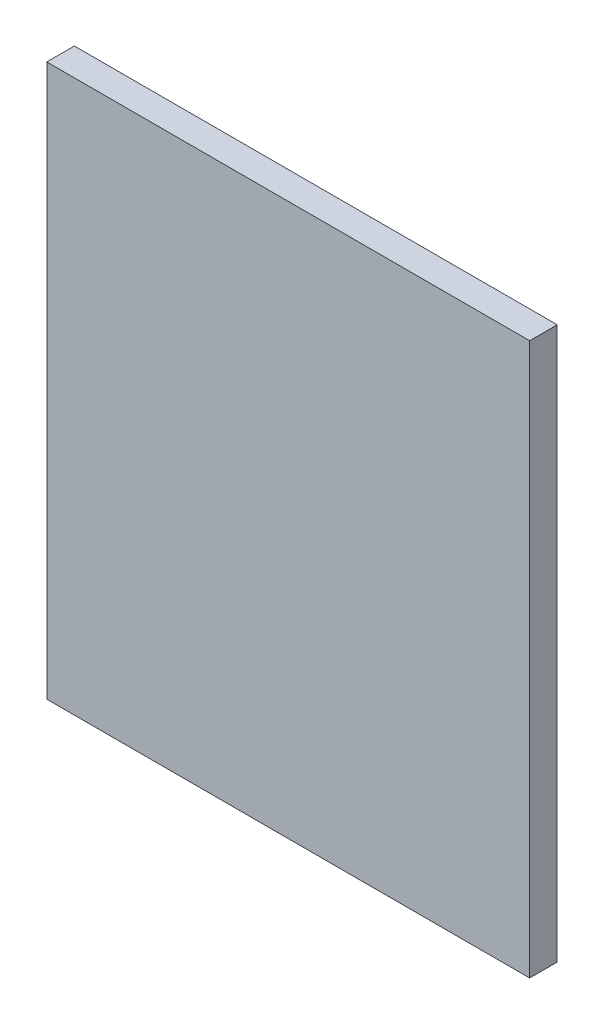
SolidWorks part; units mm, degrees
ref_plane "Front Plane" through (0, 0, 0) normal (0, 0, 1) x (1, 0, 0)
ref_plane "Top Plane" through (0, 0, 0) normal (0, 1, 0) x (1, 0, 0)
ref_plane "Right Plane" through (0, 0, 0) normal (1, 0, 0) x (0, 0, -1)
sketch "Sketch1" plane through (0, 0, 0) normal (0, 0, 1) x (1, 0, 0)
  line L1 (-175, -200) -> (175, -200)
  line L2 (-175, -200) -> (-175, 200)
  line L3 (-175, 200) -> (175, 200)
  line L4 (175, -200) -> (175, 200)
  line L5 (-175, -200) -> (175, 200) construction
  line L6 (-175, 200) -> (175, -200) construction
  point P0 (0, 0)
  dimension "D1" = 400
  dimension "D2" = 350
extrude "Boss-Extrude1" add sketch "Sketch1" along normal blind 20
